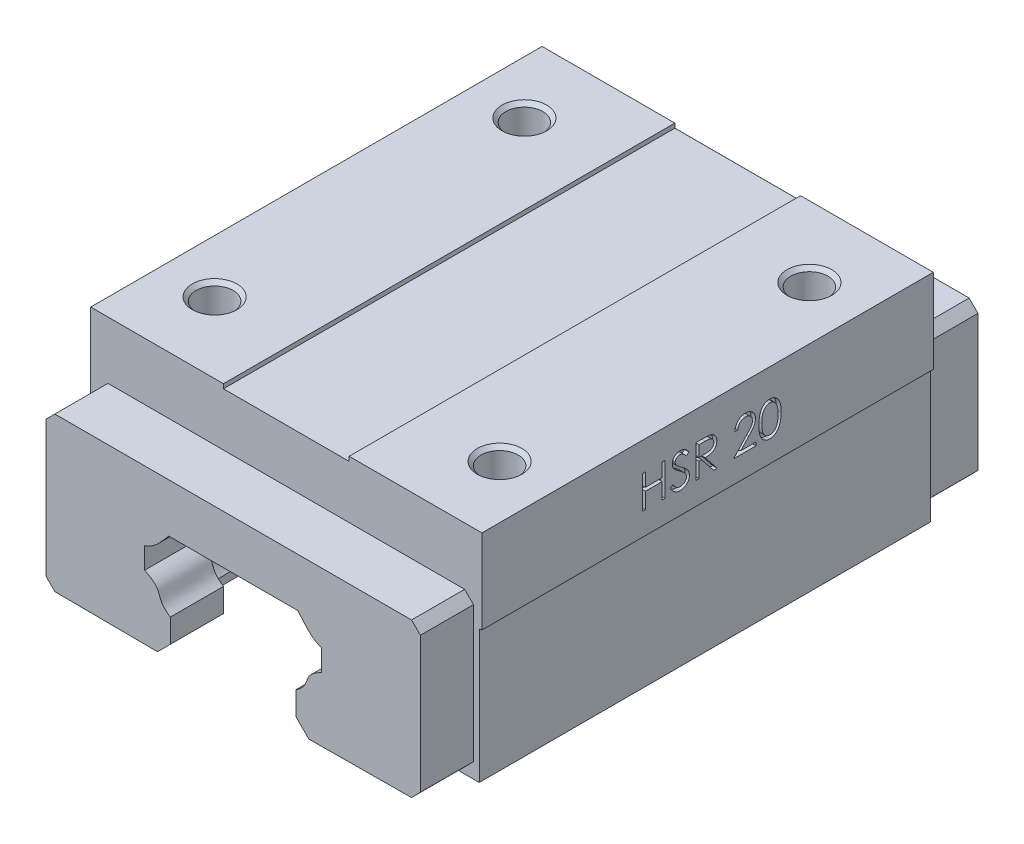
SolidWorks part; units mm, degrees
ref_plane "Front" through (0, 0, 0) normal (0, 0, 1) x (1, 0, 0)
ref_plane "Top" through (0, 0, 0) normal (0, 1, 0) x (1, 0, 0)
ref_plane "Right" through (0, 0, 0) normal (1, 0, 0) x (0, 0, -1)
sketch "Sketch1" plane through (0, 0, 0) normal (0, 0, 1) x (1, 0, 0)
  line L0 (0, 9) -> (0, -7.3495) construction
  line L1 (10, -7.9393) -> (8.9393, -9) construction
  line L2 (7.1, -1.5) -> (7.1, 1.1668) construction
  line L3 (7.2842, 9) -> (-7.2842, 9) construction
  line L4 (-10, -7.9393) -> (-10, -4.4) construction
  line L5 (10, 4.2972) -> (10, 6.7028) construction
  line L6 (7.1, -1.5) -> (10, -4.4) construction
  line L7 (-2.85, -9) -> (-8.9393, -9) construction
  line L8 (2.85, -9) -> (2.85, -7.3495) construction
  line L9 (2.85, -9) -> (8.9393, -9) construction
  line L10 (2.85, -7.3495) -> (-2.85, -7.3495) construction
  line L11 (-2.85, -9) -> (-2.85, -7.3495) construction
  line L12 (10, -7.9393) -> (10, -4.4) construction
  line L13 (-7.1, -1.5) -> (-10, -4.4) construction
  line L14 (-10, 4.2972) -> (-10, 6.7028) construction
  line L15 (-7.1, -1.5) -> (-7.1, 1.1668) construction
  line L16 (-10, -7.9393) -> (-8.9393, -9) construction
  line L17 (8.1868, 11) -> (-8.1868, 11)
  line L18 (-12, 2.9398) -> (-12, 8.1878)
  line L19 (-9.1, -0.6716) -> (-9.1, 0.2182)
  line L20 (-9.1, -0.6716) -> (-12, -3.5716)
  line L21 (-12, -3.5716) -> (-21.8, -3.5716)
  line L22 (-7.1, 21) -> (-7.1, 20.5)
  line L23 (-22.1, 21) -> (-22.1, 11.5)
  line L24 (-22.1, 21) -> (-7.1, 21)
  line L25 (-21.8, -3.5716) -> (-21.8, 11.5)
  line L26 (-21.8, 11.5) -> (-22.1, 11.5)
  line L27 (-7.1, 20.5) -> (7.1, 20.5)
  line L28 (21.8, -3.5716) -> (21.8, 11.5)
  line L29 (12, -3.5716) -> (21.8, -3.5716)
  line L30 (9.1, -0.6716) -> (12, -3.5716)
  line L31 (9.1, -0.6716) -> (9.1, 0.2182)
  line L32 (12, 2.9398) -> (12, 8.1878)
  line L33 (0.85, -11) -> (0.85, -9.3495) construction
  line L34 (-0.85, -11) -> (-0.85, -9.3495) construction
  line L35 (0.85, -9.3495) -> (-0.85, -9.3495) construction
  line L36 (0.85, -11) -> (9.7678, -11) construction
  line L37 (-0.85, -11) -> (-9.7678, -11) construction
  line L38 (12, -8.7678) -> (9.7678, -11) construction
  line L39 (12, -8.7678) -> (12, -3.5716) construction
  line L40 (-12, -8.7678) -> (-12, -3.5716) construction
  line L41 (-12, -8.7678) -> (-9.7678, -11) construction
  line L42 (22.1, 21) -> (7.1, 21)
  line L43 (22.1, 21) -> (22.1, 11.5)
  line L44 (7.1, 21) -> (7.1, 20.5)
  line L45 (22.1, 11.5) -> (21.8, 11.5)
  spline S0 degree 3 poles (-10, 6.7028) (-8.794, 7.0672) (-8.1583, 8.0094) (-7.2842, 9) knots 0 0 0 0 1 1 1 1 construction
  spline S1 degree 2 poles (-10, 4.2972) (-8.922, 3.8688) (-8.4211, 3.0233) knots 0 0 0 1 1 1 construction
  spline S2 degree 3 poles (-8.4211, 3.0233) (-8.2321, 2.4709) (-8.042, 1.7468) (-7.1, 1.1668) knots 0 0 0 0 1 1 1 1 construction
  spline S3 degree 3 poles (8.4211, 3.0233) (8.2321, 2.4709) (8.042, 1.7468) (7.1, 1.1668) knots 0 0 0 0 1 1 1 1 construction
  spline S4 degree 2 poles (10, 4.2972) (8.922, 3.8688) (8.4211, 3.0233) knots 0 0 0 1 1 1 construction
  spline S5 degree 3 poles (10, 6.7028) (8.794, 7.0672) (8.1583, 8.0094) (7.2842, 9) knots 0 0 0 0 1 1 1 1 construction
  spline S6 degree 1 poles (-12, 8.1878) (-8.1868, 11) knots 0 0 1 1 construction
  spline S7 degree 1 poles (-12, 2.9398) (-10.2262, 2.1182) knots 0 0 1 1 construction
  spline S8 degree 1 poles (-10.2262, 2.1182) (-9.1, 0.2182) knots 0 0 1 1 construction
  spline S9 degree 1 poles (10.2262, 2.1182) (9.1, 0.2182) knots 0 0 1 1 construction
  spline S10 degree 1 poles (12, 2.9398) (10.2262, 2.1182) knots 0 0 1 1 construction
  spline S11 degree 1 poles (12, 8.1878) (8.1868, 11) knots 0 0 1 1 construction
  spline S12 degree 3 poles (-8.1868, 11) (-8.3638, 10.7993) (-8.7099, 10.4111) (-9.2774, 9.7501) (-9.7045, 9.2512) (-10.0538, 8.908) (-10.2696, 8.7529) (-10.4108, 8.6803) (-10.4897, 8.6469) (-10.5507, 8.6259) (-10.5728, 8.6191) (-10.6452, 8.5972) (-10.745, 8.567) (-10.9638, 8.5009) (-11.3877, 8.3728) (-11.7557, 8.2616) (-12, 8.1878) knots -0.392908 -0.392908 -0.392908 -0.392908 -0.190329 0.01225 0.214829 0.417409 0.619988 0.721278 0.771923 0.822567 0.835229 0.84789 0.873212 0.923857 1.025147 1.227726 1.227726 1.227726 1.227726
  spline S13 degree 3 poles (-12, 2.9398) (-11.7653, 2.8465) (-11.4057, 2.7037) (-11.0127, 2.5473) (-10.7501, 2.4433) (-10.6297, 2.3941) (-10.4971, 2.328) (-10.3368, 2.2259) (-10.2727, 2.1693) (-10.2262, 2.1182) knots -0.585105 -0.585105 -0.585105 -0.585105 -0.258531 -0.095244 -0.013601 0.068043 0.231329 0.394616 0.72119 0.72119 0.72119 0.72119
  spline S14 degree 3 poles (-10.2262, 2.1182) (-10.1816, 1.9887) (-10.0985, 1.7573) (-9.8775, 1.2665) (-9.5629, 0.7459) (-9.2592, 0.3811) (-9.1, 0.2182) knots 0.146752 0.146752 0.146752 0.146752 0.298579 0.450406 0.602232 0.754059 0.754059 0.754059 0.754059
  spline S15 degree 3 poles (9.1, 0.2182) (9.2592, 0.3811) (9.5629, 0.7459) (9.8775, 1.2665) (10.0985, 1.7573) (10.1816, 1.9887) (10.2262, 2.1182) knots 0.146752 0.146752 0.146752 0.146752 0.298579 0.450406 0.602232 0.754059 0.754059 0.754059 0.754059
  spline S16 degree 3 poles (10.2262, 2.1182) (10.2727, 2.1693) (10.3368, 2.2259) (10.4971, 2.328) (10.6297, 2.3941) (10.7501, 2.4433) (11.0127, 2.5473) (11.4057, 2.7037) (11.7653, 2.8465) (12, 2.9398) knots -0.585105 -0.585105 -0.585105 -0.585105 -0.258531 -0.095244 0.068043 0.149686 0.231329 0.394616 0.72119 0.72119 0.72119 0.72119
  spline S17 degree 3 poles (12, 8.1878) (11.7557, 8.2616) (11.3877, 8.3728) (10.9638, 8.5009) (10.745, 8.567) (10.6452, 8.5972) (10.5728, 8.6191) (10.5507, 8.6259) (10.4897, 8.6469) (10.4108, 8.6803) (10.2696, 8.7529) (10.0538, 8.908) (9.7045, 9.2512) (9.2774, 9.7501) (8.7099, 10.4111) (8.3638, 10.7993) (8.1868, 11) knots -0.392908 -0.392908 -0.392908 -0.392908 -0.190329 -0.089039 -0.038395 -0.013072 -0.000411 0.01225 0.062895 0.11354 0.214829 0.417409 0.619988 0.822567 1.025147 1.227726 1.227726 1.227726 1.227726
  dimension "D14" = 0.5
  dimension "D1" = 10
  dimension "D2" = 18
  dimension "D3" = 7.5
  dimension "D4" = 7.1
  dimension "D5" = 135
  dimension "D6" = 1.5
  dimension "D7" = 45
  dimension "D8" = 2.4057
  dimension "D10" = 15
  dimension "D11" = 22.1
  dimension "D12" = 21.8
  dimension "D13" = 9.5
  dimension "D16" = 30
  dimension "D9" = 2
extrude "Boss-Extrude1" add sketch "Sketch1" against normal blind 51 contours L42 L44 L27 L22 L24 L23 L26 L25 L21 L20 L19 S14 S13 L18 S12 L17 S17 L32 S16 S15 L31 L30 L29 L28 L45 L43
hole_wizard "M5 Tapped Hole1" positions "3DSketch1" profile "Sketch3" tap size "M5" standard "ISO"
sketch3d "3DSketch1"
  line L0 (-22.1, 21, -51) -> (-7.1, 21, -51) construction
  line L1 (-22.1, 21, -51) -> (-22.1, 21, 0) construction
  point P0 (-16.1, 21, -43)
  dimension "D1" = 8
  dimension "D2" = 6
sketch "Sketch3" plane through (-16.1, 21, -43) normal (1, 0, 0) x (0, 0, 1)
  line L0 (0, 0) -> (0, 9.2618)
  line L1 (0, 9.2618) -> (2.1, 8)
  line L2 (2.1, 8) -> (2.1, 0.425)
  line L3 (2.1, 0.425) -> (2.525, 0)
  line L5 (2.525, 0) -> (0, 0)
  line L6 (-2.1, 0.425) -> (-2.525, 0) construction
  line L10 (0, 9.2618) -> (-2.1, 8) construction
  line L11 (0, -6.35) -> (0, 107.95) construction
  dimension "Tap Drill Dia." = 4.2
  dimension "Tap Drill Depth" = 8
  dimension "Near C'Sink Dia." = 5.05
  dimension "Near C'Sink Angle" = 90
  dimension "Drill Angle" = 118
cosmetic thread "Hole Thread1" parameters "D1"=8, "D2"=5
ref_plane "Plane1" through (0, 0, -25.5) normal (0, 0, -1) x (-1, 0, 0)
mirror "Mirror1" about plane through (0, 0, -25.5) normal (0, 0, -1) of "M5 Tapped Hole1"
ref_plane "Plane2" through (0, 0, 0) normal (-1, 0, 0) x (0, 0, 1)
mirror "Mirror2" about plane through (0, 0, 0) normal (-1, 0, 0) of "Mirror1", "M5 Tapped Hole1"
sketch "Sketch5" plane through (0, 0, 0) normal (0, 0, 1) x (1, 0, 0)
  line L0 (0, 14.5076) -> (-21.1498, 14.5076)
  line L1 (-21.1498, -2.8646) -> (-8.55, -2.95)
  line L2 (-21.1498, 14.5076) -> (-21.1498, -2.8646)
  line L3 (-7.1, -1.5) -> (-10, -4.4) construction
  line L4 (-8.55, -2.95) -> (-7.1, -1.5)
  line L5 (-7.1, -1.5) -> (-7.1, 1.1668)
  line L6 (-10, 4.2972) -> (-10, 6.7028)
  line L7 (-7.2842, 9) -> (7.2842, 9)
  line L8 (0, 9) -> (0, -7.3495) construction
  line L9 (10, 4.2972) -> (10, 6.7028)
  line L10 (7.1, -1.5) -> (7.1, 1.1668)
  line L11 (8.55, -2.95) -> (7.1, -1.5)
  line L12 (21.1498, 14.5076) -> (21.1498, -2.8646)
  line L13 (21.1498, -2.8646) -> (8.55, -2.95)
  line L14 (0, 14.5076) -> (21.1498, 14.5076)
  spline S0 degree 3 poles (-10, 4.2972) (-7.5431, 3.077) (-9.0188, 2.3999) (-7.1, 1.1668) knots 0 0 0 0 1 1 1 1
  spline S1 degree 3 poles (-10, 6.7028) (-9.5803, 6.8352) (-9.1586, 7.065) (-8.2451, 7.8442) (-7.926, 8.2753) (-7.2842, 9) knots 0 0 0 0 0.3782 0.4782 1 1 1 1
  spline S2 degree 3 poles (10, 6.7028) (9.5803, 6.8352) (9.1586, 7.065) (8.2451, 7.8442) (7.926, 8.2753) (7.2842, 9) knots 0 0 0 0 0.3782 0.4782 1 1 1 1
  spline S3 degree 3 poles (10, 4.2972) (7.5431, 3.077) (9.0188, 2.3999) (7.1, 1.1668) knots 0 0 0 0 1 1 1 1
  point P4 (0, 14.5076)
extrude "Boss-Extrude3" add sketch "Sketch5" along normal blind 6
chamfer "Chamfer1" distance 1 angle 45 4 edges at (-21.1498, -2.8646, 3) (21.1498, -2.8646, 3) (21.1498, 14.5076, 3) (-21.1498, 14.5076, 3)
mirror "Mirror4" about plane through (0, 0, -25.5) normal (0, 0, -1) of "Chamfer1", "Boss-Extrude3"
sketch "Sketch6" plane through (22.1, 0, 0) normal (1, 0, 0) x (0, 0, -1)
  text T0 "HSR 20" font "Century Gothic" height in points 14
extrude "Cut-Extrude1" cut sketch "Sketch6" against normal blind 0.5
